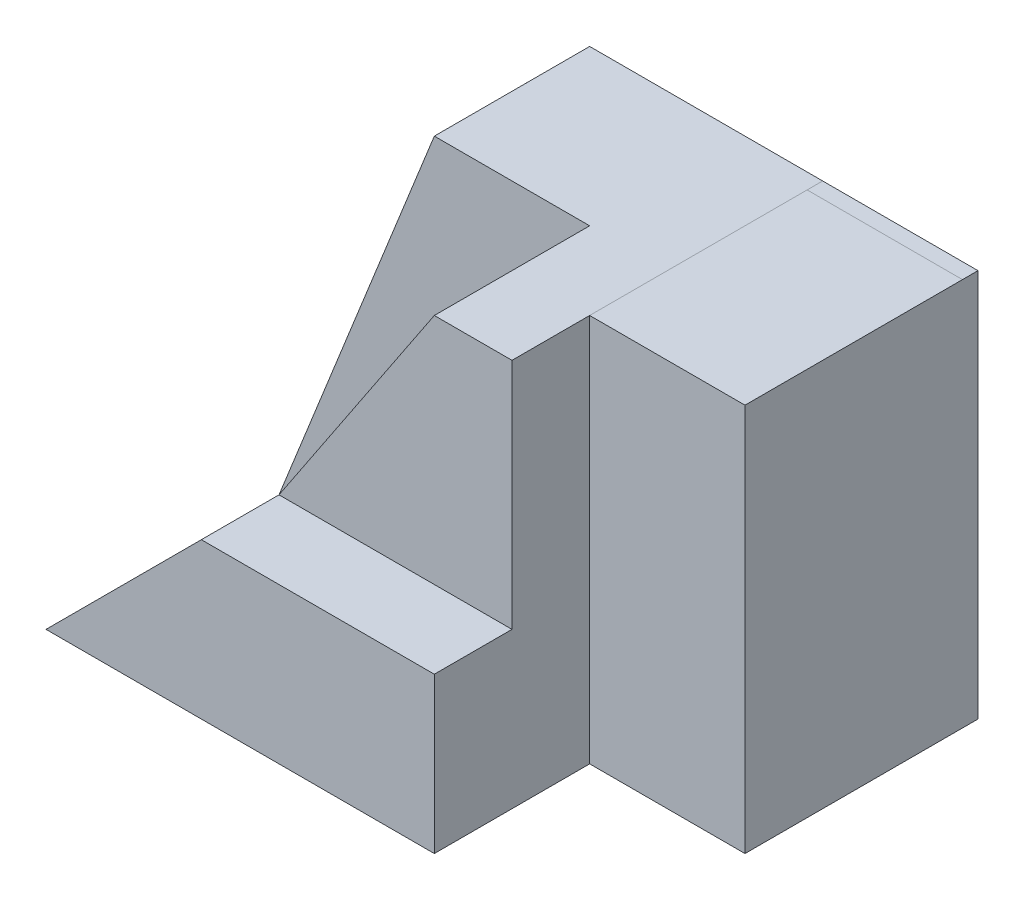
SolidWorks part; units mm, degrees
ref_plane "Front Plane" through (0, 0, 0) normal (0, 0, 1) x (1, 0, 0)
ref_plane "Top Plane" through (0, 0, 0) normal (0, 1, 0) x (1, 0, 0)
ref_plane "Right Plane" through (0, 0, 0) normal (1, 0, 0) x (0, 0, -1)
sketch "Sketch1" plane through (0, 0, 0) normal (0, 0, 1) x (1, 0, 0)
  line L1 (0, 0) -> (70, 0)
  line L2 (0, 0) -> (0, 50)
  line L3 (0, 50) -> (70, 50)
  line L4 (70, 0) -> (70, 50)
  dimension "D1" = 70
  dimension "D2" = 50
extrude "Boss-Extrude1" add sketch "Sketch1" along normal blind 50
sketch "Sketch2" plane through (0, 0, 50) normal (0, 0, 1) x (1, 0, 0)
  line L0 (0, 0) -> (20, 50)
  line L1 (70, 50) -> (0, 50) construction
  line L2 (20, 50) -> (0, 50)
  line L3 (0, 50) -> (0, 0)
  dimension "D1" = 20
extrude "Cut-Extrude1" cut sketch "Sketch2" against normal blind 50
sketch "Sketch3" plane through (70, 0, 0) normal (1, 0, 0) x (0, 0, -1)
  line L1 (-50, 50) -> (-40, 50)
  line L2 (-50, 50) -> (-50, 20)
  line L3 (-50, 20) -> (-40, 20)
  line L4 (-40, 50) -> (-40, 20)
  dimension "D1" = 10
  dimension "D2" = 30
extrude "Cut-Extrude2" cut sketch "Sketch3" against normal blind 121
sketch "Sketch4" plane through (0, 0, 0) normal (0, -1, 0) x (1, 0, 0)
  line L1 (70, 50) -> (50, 50)
  line L2 (70, 50) -> (70, 30)
  line L3 (70, 30) -> (50, 30)
  line L4 (50, 50) -> (50, 30)
  dimension "D1" = 20
  dimension "D2" = 20
extrude "Cut-Extrude3" cut sketch "Sketch4" against normal blind 121
sketch "Sketch5" plane through (0, 0, 50) normal (0, 0, 1) x (1, 0, 0)
  line L0 (0, 0) -> (20, 20)
  line L1 (8, 20) -> (50, 20) construction
  line L2 (20, 20) -> (40, 50)
  line L3 (40, 50) -> (20, 50)
  line L4 (20, 50) -> (0, 0)
  dimension "D1" = 20
  dimension "D2" = 10
  dimension "D3" = 50
  dimension "D4" = 20
extrude "Cut-Extrude8" cut sketch "Sketch5" against normal blind 30
sketch "Sketch10" plane through (0, 50, 0) normal (0, 1, 0) x (1, 0, 0)
  line L0 (20, 0) -> (50, 0)
  line L1 (70, 0) -> (20, 0) construction
  line L2 (50, 0) -> (50, -40)
  line L3 (50, -40) -> (40, -40)
  line L4 (40, -40) -> (50, -40) construction
  line L5 (40, -40) -> (40, -10)
  line L6 (40, -10) -> (20, -10)
  line L7 (20, 0) -> (20, -20) construction
  line L8 (20, -10) -> (20, 0)
  dimension "D1" = 30
  dimension "D2" = 40
  dimension "D3" = 10
  dimension "D4" = 30
extrude "Cut-Extrude9" cut sketch "Sketch10" against normal blind 0.0001
sketch "Sketch11" plane through (0, 50, 0) normal (0, 1, 0) x (1, 0, 0)
  line L0 (50, 0) -> (70, 0)
  line L1 (70, 0) -> (70, -2)
  line L2 (70, -30) -> (70, 0) construction
  line L3 (70, -2) -> (50, -2)
  line L4 (50, -30) -> (50, 0) construction
  line L5 (50, -2) -> (50, 0)
  dimension "D1" = 2
extrude "Boss-Extrude8" add sketch "Sketch11" along normal blind 0.0001
ref_plane "Plane1" through (0, 50, 0) normal (0, 1, 0) x (1, 0, 0)
sketch "Sketch12" plane through (0, 50, 0) normal (0, 1, 0) x (1, 0, 0)
  line L0 (40, -20) -> (40, -40) construction
  line L1 (20, -10) -> (40, -10)
  line L2 (20, -10) -> (20, -30)
  line L3 (20, -30) -> (40, -30)
  line L4 (40, -10) -> (40, -30)
extrude "Cut-Extrude10" cut sketch "Sketch12" against normal blind 0.0001
sketch "Sketch14" plane through (0, 0, 0) normal (-0.7071, 0.7071, 0) x (0, 0, 1)
  line L0 (20, 28.2843) -> (50, 28.2843)
  line L1 (50, 28.2843) -> (50, 0)
  line L2 (50, 0) -> (30, 0)
  line L3 (50, 0) -> (20, 0) construction
  line L4 (30, 0) -> (20, 28.2843)
  dimension "D1" = 20
extrude "Cut-Extrude11" cut sketch "Sketch14" against normal blind 0.001
sketch "Sketch15" plane through (0, 0, 0) normal (-0.9285, 0.3714, 0) x (0, 0, 1)
  line L0 (0, 53.8516) -> (30, 0)
  line L1 (30, 0) -> (0, 0)
  line L2 (0, 0) -> (0, 53.8516)
  dimension "D1" = 30
extrude "Cut-Extrude12" cut sketch "Sketch15" against normal blind 0.001
sketch "Sketch16" plane through (0.0009, -0.0004, 0) normal (-0.9285, 0.3714, 0) x (0, 0, 1)
  line L0 (20, 17.9505) -> (29.9987, 0.0023)
  line L1 (29.9987, 0.0023) -> (20, 0.0023)
  line L2 (20, 0.0023) -> (20, 17.9505)
  line L3 (50, 0.0005) -> (29.9996, 0.0005) construction
  line L4 (20, 17.9505) -> (0, 53.8516) construction
extrude "Cut-Extrude13" cut sketch "Sketch16" against normal blind 9.001
sketch "Sketch17" plane through (0, 0, 0) normal (-0.7071, 0.7071, 0) x (0, 0, 1)
  line L0 (20, 28.2843) -> (20, 19.5296)
  line L1 (20, 19.5296) -> (30, 0)
  line L2 (30, 0) -> (20, 28.2843)
extrude "Boss-Extrude14" add sketch "Sketch17" along normal blind 0.0002
sketch "Sketch18" plane through (0.0007, -0.0007, 0) normal (-0.7071, 0.7071, 0) x (0, 0, 1)
  line L1 (50, 28.2843) -> (20, 28.2843)
  line L2 (50, 28.2843) -> (50, 0)
  line L3 (50, 0) -> (20, 0)
  line L4 (20, 28.2843) -> (20, 0)
  dimension "D1" = 30
  dimension "D2" = 28.2843
extrude "Cut-Extrude17" cut sketch "Sketch18" along normal blind 23.0002
sketch "Sketch19" plane through (0, 0, 0) normal (-0.9285, 0.3714, 0) x (0, 0, 1)
  line L0 (17.2146, 22.9505) -> (20, 22.9505)
  line L1 (20, 17.9505) -> (0, 53.8516) construction
  line L2 (20, 53.8516) -> (20, 17.9505) construction
  line L3 (20, 22.9505) -> (20, 17.9505)
  line L4 (20, 17.9505) -> (17.2146, 22.9505)
  dimension "D1" = 5
extrude "Cut-Extrude18" cut sketch "Sketch19" against normal blind 0.0001
